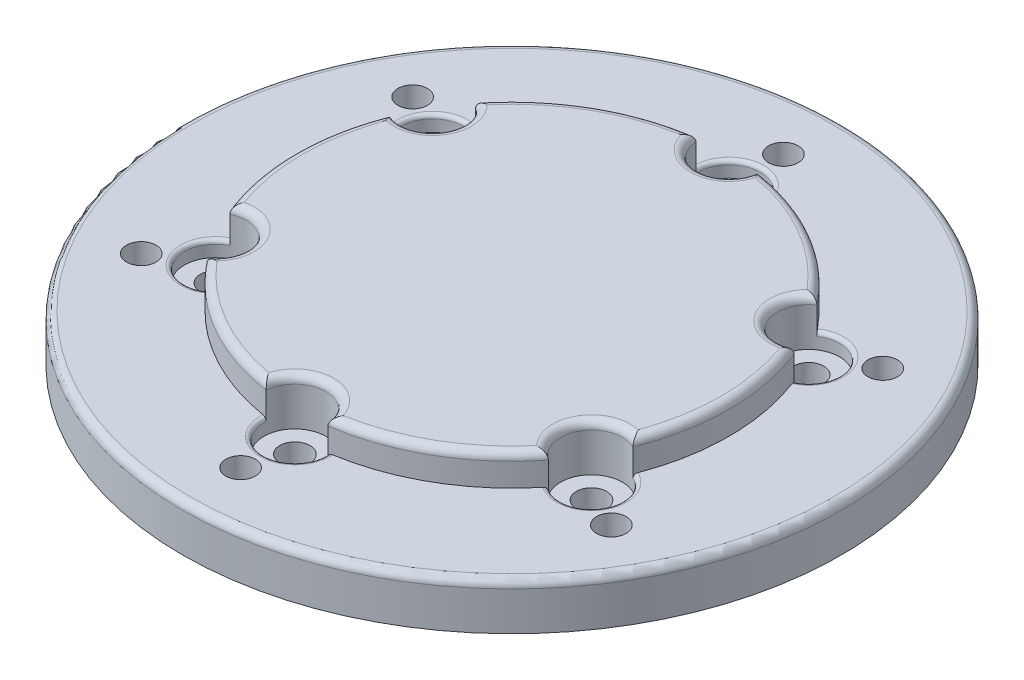
SolidWorks part; units mm, degrees
ref_plane "Front Plane" through (0, 0, 0) normal (0, 0, 1) x (1, 0, 0)
ref_plane "Top Plane" through (0, 0, 0) normal (0, 1, 0) x (1, 0, 0)
ref_plane "Right Plane" through (0, 0, 0) normal (1, 0, 0) x (0, 0, -1)
sketch "Sketch1" plane through (0, 0, 0) normal (0, 1, 0) x (1, 0, 0)
  circle A0 centre (0, 0) radius 42.5
extrude "Boss-Extrude1" add sketch "Sketch1" along normal blind 6
sketch "Sketch2" plane through (0, 6, 0) normal (0, 1, 0) x (1, 0, 0)
  line L0 (0, 0) -> (0, 35) construction
  line L1 (0, 0) -> (-30.3109, 17.5) construction
  line L2 (0, 0) -> (-30.3109, -17.5) construction
  line L3 (0, 0) -> (0, -35) construction
  line L4 (0, 0) -> (30.3109, -17.5) construction
  line L5 (0, 0) -> (30.3109, 17.5) construction
  circle A1 centre (0, 35) radius 1.9
  circle A2 centre (-30.3109, 17.5) radius 1.9
  circle A3 centre (30.3109, 17.5) radius 1.9
  circle A4 centre (30.3109, -17.5) radius 1.9
  circle A5 centre (-30.3109, -17.5) radius 1.9
  circle A6 centre (0, -35) radius 1.9
extrude "Cut-Extrude1" cut sketch "Sketch2" against normal blind 34
sketch "Sketch3" plane through (0, 0, 0) normal (0, -1, 0) x (1, 0, 0)
  circle A0 centre (0, -35) radius 4
  circle A1 centre (-30.3109, -17.5) radius 4
  circle A2 centre (-30.3109, 17.5) radius 4
  circle A3 centre (0, 35) radius 4
  circle A4 centre (30.3109, 17.5) radius 4
  circle A5 centre (30.3109, -17.5) radius 4
extrude "Cut-Extrude2" cut sketch "Sketch3" against normal blind 2.5
sketch "Sketch4" plane through (0, 6, 0) normal (0, 1, 0) x (1, 0, 0)
  circle A0 centre (0, 0) radius 28
extrude "Boss-Extrude2" add sketch "Sketch4" along normal blind 4
sketch "Sketch5" plane through (0, 10, 0) normal (0, 1, 0) x (1, 0, 0)
  line L0 (0, 0) -> (-30.3109, 17.5) construction
  line L1 (0, 0) -> (0, 35) construction
  line L2 (0, 0) -> (30.3109, 17.5) construction
  line L3 (0, 0) -> (30.3109, -17.5) construction
  line L4 (0, 0) -> (0, -35) construction
  line L5 (0, 0) -> (-30.3109, -17.5) construction
  circle A0 centre (-24.2487, 14) radius 1.95
  circle A1 centre (0, 0) radius 28 construction
  circle A2 centre (0, 28) radius 1.95
  circle A3 centre (24.2487, 14) radius 1.95
  circle A4 centre (24.2487, -14) radius 1.95
  circle A5 centre (0, -28) radius 1.95
  circle A6 centre (-24.2487, -14) radius 1.95
extrude "Cut-Extrude3" cut sketch "Sketch5" against normal blind 18
sketch "Sketch6" plane through (0, 10, 0) normal (0, 1, 0) x (1, 0, 0)
  circle A0 centre (0, 28) radius 4
  circle A1 centre (24.2487, 14) radius 4
  circle A2 centre (24.2487, -14) radius 4
  circle A3 centre (0, -28) radius 4
  circle A4 centre (-24.2487, -14) radius 4
  circle A5 centre (-24.2487, 14) radius 4
extrude "Cut-Extrude4" cut sketch "Sketch6" against normal blind 6
fillet "Fillet3" radius 1 12 edges at (28, 10, 0) (20.7846, 10, 12) (14, 10, 24.2487) (0, 10, 24) (-14, 10, 24.2487) (-20.7846, 10, 12) (-28, 10, 0) (-20.7846, 10, -12) (-14, 10, -24.2487) (0, 10, -24) (14, 10, -24.2487) (20.7846, 10, -12)
fillet "Fillet4" radius 0.5 6 edges at (-27.7128, 6, -16) (0, 6, -32) (27.7128, 6, -16) (27.7128, 6, 16) (0, 6, 32) (-27.7128, 6, 16)
sketch "Sketch8" plane through (0, 0, 0) normal (0, -1, 0) x (1, 0, 0)
  circle A0 centre (0, 35) radius 1.9
  circle A1 centre (0, 35) radius 2.1
  circle A2 centre (30.3109, 17.5) radius 1.9
  circle A3 centre (30.3109, 17.5) radius 2.1
  circle A4 centre (30.3109, -17.5) radius 1.9
  circle A5 centre (30.3109, -17.5) radius 2.1
  circle A6 centre (0, -35) radius 1.9
  circle A7 centre (0, -35) radius 2.1
  circle A8 centre (-30.3109, -17.5) radius 1.9
  circle A9 centre (-30.3109, -17.5) radius 2.1
  circle A10 centre (-30.3109, 17.5) radius 1.9
  circle A11 centre (-30.3109, 17.5) radius 2.1
extrude "Boss-Extrude3" add sketch "Sketch8" against normal blind 4
sketch "Sketch9" plane through (0, 0, 0) normal (0, -1, 0) x (1, 0, 0)
  circle A0 centre (0, 35) radius 3
  circle A1 centre (30.3109, 17.5) radius 3
  circle A2 centre (30.3109, -17.5) radius 3
  circle A3 centre (0, -35) radius 3
  circle A4 centre (-30.3109, -17.5) radius 3
  circle A5 centre (-30.3109, 17.5) radius 3
extrude "Boss-Extrude4" add sketch "Sketch9" against normal blind 0.4
fillet "Fillet5" radius 1 1 edges at (0, 6, 42.5)
